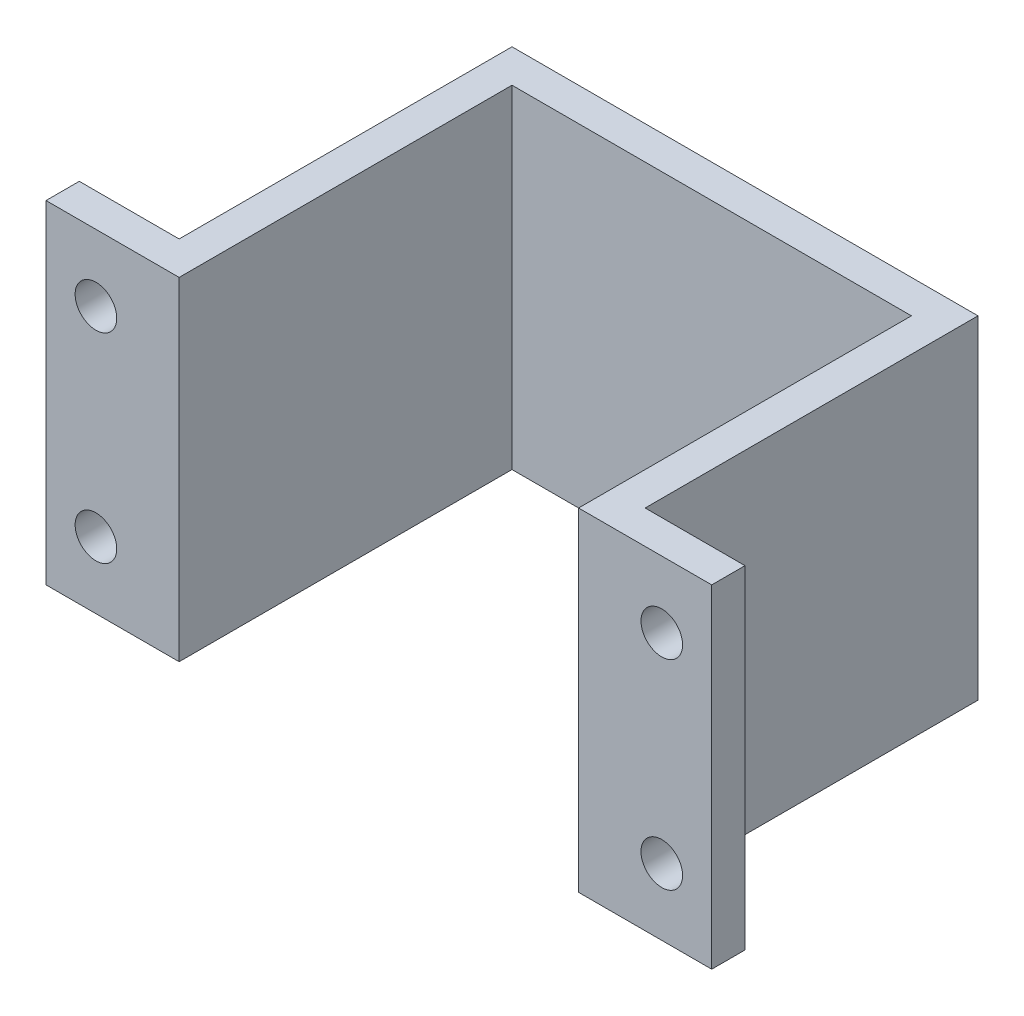
SolidWorks part; units mm, degrees
material "6061 合金"
ref_plane "前视基准面" through (0, 0, 0) normal (0, 0, 1) x (1, 0, 0)
ref_plane "上视基准面" through (0, 0, 0) normal (0, 1, 0) x (1, 0, 0)
ref_plane "右视基准面" through (0, 0, 0) normal (1, 0, 0) x (0, 0, -1)
sketch "草图2" plane through (0, 0, 0) normal (0, 1, 0) x (1, 0, 0)
  line L0 (0, 0) -> (0, 51.254) construction
  line L1 (7, 11) -> (-7, 11)
  line L2 (-7, 11) -> (-7, 1)
  line L3 (-7, 1) -> (-10, 1)
  line L4 (-10, 1) -> (-10, 0)
  line L5 (-10, 0) -> (-6, 0)
  line L6 (-6, 0) -> (-6, 10)
  line L7 (-6, 10) -> (6, 10)
  line L8 (6, 0) -> (6, 10)
  line L9 (10, 0) -> (6, 0)
  line L10 (10, 1) -> (10, 0)
  line L11 (7, 1) -> (10, 1)
  line L12 (7, 11) -> (7, 1)
  point P12 (0, 10)
  point P17 (0, 11)
  dimension "D1" = 1
  dimension "D2" = 3
  dimension "D3" = 1
  dimension "D4" = 6
  dimension "D5" = 1
  dimension "D6" = 10
extrude "凸台-拉伸1" add sketch "草图2" along normal blind 10
hole_wizard "M1.6 螺纹孔1" positions "草图4" profile "草图3" tap size "M1.6" standard "Gb"
sketch "草图4" plane through (0, 0, -1) normal (0, 0, -1) x (-1, 0, 0)
  line L0 (-10, 5) -> (10, 5) construction
  line L1 (-10, 10) -> (-10, 0) construction
  line L2 (10, 10) -> (10, 0) construction
  line L5 (0, 10) -> (0, 0) construction
  line L6 (-7, 10) -> (7, 10) construction
  line L9 (-10, 10) -> (-7, 10) construction
  point P0 (-8.5, 8)
  point P19 (-8.5, 10)
  point P22 (8.5, 8)
  point P23 (8.5, 2)
  point P24 (-8.5, 2)
  dimension "D1" = 2
  dimension "D2" = 1.5
  dimension "D3" = 17
  dimension "D4" = 6
sketch "草图3" plane through (8.5, 8, -1) normal (1, 0, 0) x (0, 1, 0)
  line L0 (0, 0) -> (0, 5.3255)
  line L1 (0, 5.3255) -> (0.625, 4.95)
  line L2 (0.625, 4.95) -> (0.625, 0)
  line L5 (0.625, 0) -> (0, 0)
  line L10 (0, 5.3255) -> (-0.625, 4.95) construction
  line L11 (0, -6.35) -> (0, 107.95) construction
  dimension "螺纹孔钻头直径" = 1.25
  dimension "螺纹孔钻头深度" = 4.95
  dimension "导头角度" = 118
cosmetic thread "孔螺蚊线1" parameters "D1"=2, "D2"=1.6
cosmetic thread "孔螺蚊线2" parameters "D1"=2, "D2"=1.6
cosmetic thread "孔螺蚊线3" parameters "D1"=2, "D2"=1.6
cosmetic thread "孔螺蚊线4" parameters "D1"=2, "D2"=1.6
